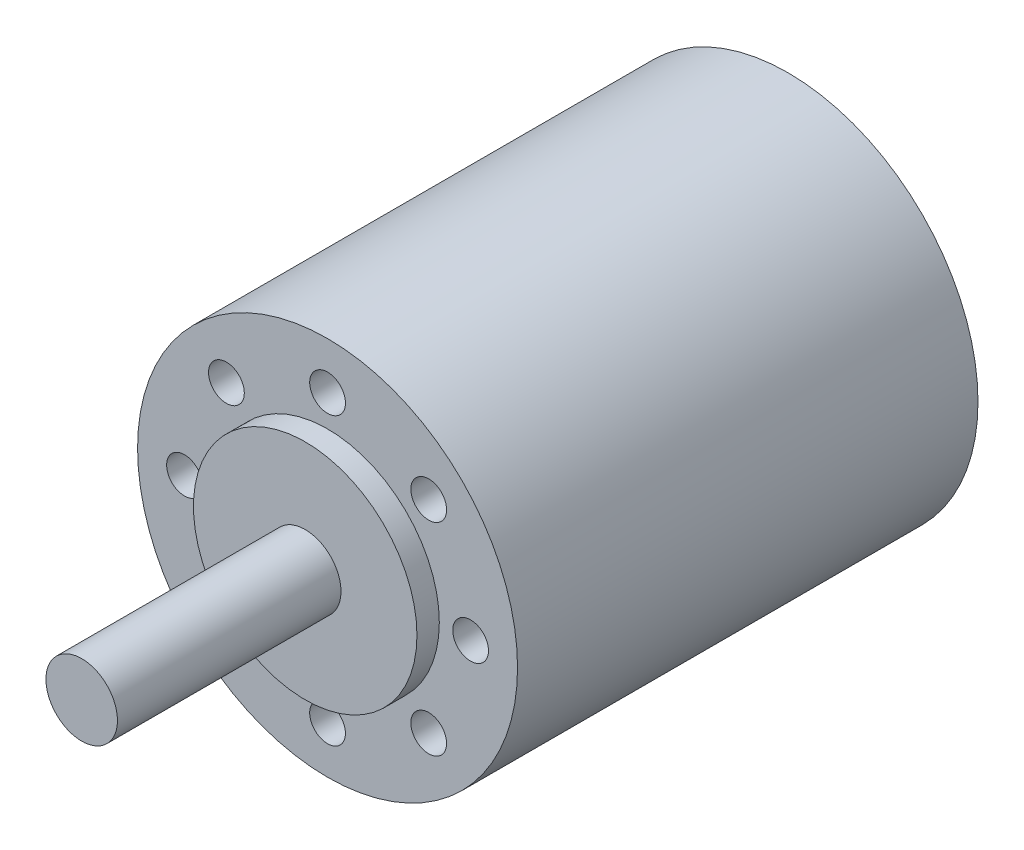
SolidWorks part; units mm, degrees
material "1.4000 (X6Cr13)"
ref_plane "前基準面" through (0, 0, 0) normal (0, 0, 1) x (1, 0, 0)
ref_plane "上基準面" through (0, 0, 0) normal (0, 1, 0) x (1, 0, 0)
ref_plane "右基準面" through (0, 0, 0) normal (1, 0, 0) x (0, 0, -1)
sketch "草圖1" plane through (0, 0, 0) normal (0, 0, 1) x (1, 0, 0)
  circle A0 centre (0, 0) radius 21.25
extrude "填料-伸長1" add sketch "草圖1" along normal blind 51.5
sketch "草圖2" plane through (0, 0, 0) normal (0, 0, -1) x (-1, 0, 0)
  circle A1 centre (0, 12.5) radius 1.5
  circle A2 centre (0, -12.5) radius 1.5
extrude "填料-伸長2" add sketch "草圖2" along normal blind 4
sketch "草圖3" plane through (0, 0, 0) normal (0, 0, -1) x (-1, 0, 0)
  circle A0 centre (0, 0) radius 8.75
extrude "除料-伸長1" cut sketch "草圖3" against normal blind 1.5
sketch "草圖4" plane through (0, 0, 1.5) normal (0, 0, -1) x (-1, 0, 0)
  circle A0 centre (0, 0) radius 2.5
extrude "除料-伸長2" cut sketch "草圖4" against normal blind 6.3
sketch "草圖5" plane through (0, 0, 7.8) normal (0, 0, -1) x (-1, 0, 0)
  circle A0 centre (0, 0) radius 2
extrude "除料-伸長3" cut sketch "草圖5" against normal blind 7
sketch "草圖7" plane through (0, 0, 51.5) normal (0, 0, 1) x (1, 0, 0)
  circle A0 centre (0, 0) radius 12.5
extrude "填料-伸長3" add sketch "草圖7" along normal blind 2.5
sketch "草圖11" plane through (0, 0, 54) normal (0, 0, 1) x (1, 0, 0)
  circle A0 centre (0, 0) radius 4
extrude "填料-伸長5" add sketch "草圖11" along normal blind 25
ref_plane "平面1" through (0, -4, 0) normal (0, -1, 0) x (-1, 0, 0)
sketch "草圖12" plane through (0, -4, 0) normal (0, 1, 0) x (1, 0, 0)
  line L6 (-1.65, -74.85) -> (-1.65, -58.15)
  line L8 (1.65, -58.15) -> (1.65, -74.85)
  arc A0 (1.65, -58.15) -> (-1.65, -58.15) centre (0, -58.15) ccw
  arc A1 (-1.65, -74.85) -> (1.65, -74.85) centre (0, -74.85) ccw
extrude "除料-伸長11" cut sketch "草圖12" along normal blind 3.5
sketch "草圖13" plane through (0, 0, 51.5) normal (0, 0, 1) x (1, 0, 0)
  circle A1 centre (16, 0) radius 2
  circle A2 centre (0, -16) radius 2
  circle A3 centre (-16, 0) radius 2
  circle A4 centre (0, 16) radius 2
  circle A8 centre (11.3137, 11.3137) radius 2
  circle A9 centre (11.3137, -11.3137) radius 2
  circle A10 centre (-11.3137, -11.3137) radius 2
  circle A11 centre (-11.3137, 11.3137) radius 2
extrude "除料-伸長10" cut sketch "草圖13" against normal blind 7
